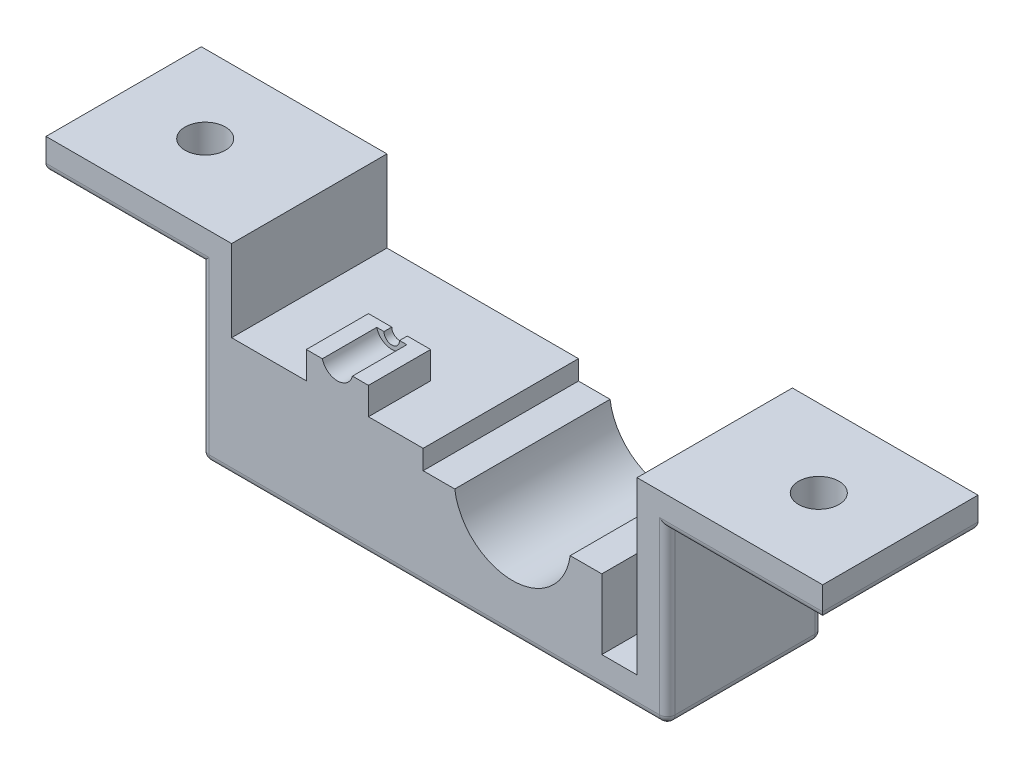
SolidWorks part; units mm, degrees
ref_plane "前视基准面" through (0, 0, 0) normal (0, 0, 1) x (1, 0, 0)
ref_plane "上视基准面" through (0, 0, 0) normal (0, 1, 0) x (1, 0, 0)
ref_plane "右视基准面" through (0, 0, 0) normal (1, 0, 0) x (0, 0, -1)
sketch "草图1" plane through (0, 0, 0) normal (0, 0, 1) x (1, 0, 0)
  line L1 (-24.7617, 11.9489) -> (35.2383, 11.9489)
  line L2 (-24.7617, 11.9489) -> (-24.7617, -14.0511)
  line L3 (-24.7617, -14.0511) -> (35.2383, -14.0511)
  line L4 (35.2383, 11.9489) -> (35.2383, -14.0511)
  dimension "D1" = 60
  dimension "D2" = 26
extrude "凸台-拉伸1" add sketch "草图1" against normal blind 24
sketch "草图2" plane through (0, 0, 0) normal (0, 0, 1) x (1, 0, 0)
  line L0 (-20.7617, -10.0511) -> (31.2383, -10.0511)
  line L1 (-24.7617, 11.9489) -> (-24.7617, -14.0511) construction
  line L2 (35.2383, -14.0511) -> (35.2383, 11.9489) construction
  line L3 (31.2383, 11.9489) -> (31.2383, -10.0511)
  line L4 (35.2383, 11.9489) -> (-24.7617, 11.9489) construction
  line L5 (-20.7617, 11.9489) -> (-20.7617, -10.0511)
  line L6 (-24.7617, -14.0511) -> (35.2383, -14.0511) construction
  dimension "D1" = 4
  dimension "D2" = 4
  dimension "D3" = 4
extrude "切除-拉伸1" cut sketch "草图2" against normal blind 24 and the other way through all
sketch "草图3" plane through (0, -10.0511, 0) normal (0, 1, 0) x (1, 0, 0)
  line L0 (26.7983, 0) -> (26.7983, 24)
  line L1 (-20.7617, 0) -> (31.2383, 0) construction
  line L2 (-20.7617, 24) -> (31.2383, 24) construction
  line L3 (31.2383, 0) -> (31.2383, 24) construction
  line L4 (3.7983, 0) -> (3.7983, 24)
  line L5 (3.7983, 0) -> (26.7983, 0)
  line L6 (26.7983, 24) -> (3.7983, 24)
  dimension "D1" = 4.44
  dimension "D2" = 23
extrude "凸台-拉伸2" add sketch "草图3" along normal blind 10
sketch "草图4" plane through (0, 0, 0) normal (0, 0, 1) x (1, 0, 0)
  line L0 (3.7983, -0.0511) -> (26.7983, -0.0511) construction
  line L1 (7.7983, -0.0511) -> (22.7983, -0.0511)
  arc A0 (7.7983, -0.0511) -> (22.7983, -0.0511) centre (15.2983, -0.0511) ccw
  dimension "D1" = 15
extrude "切除-拉伸2" cut sketch "草图4" against normal through all
sketch "草图5" plane through (0, 0, 0) normal (0, 0, 1) x (1, 0, 0)
  line L0 (3.7983, -1.0511) -> (26.7983, -1.0511)
  line L1 (3.7983, -0.0511) -> (3.7983, -10.0511) construction
  line L2 (26.7983, -0.0511) -> (26.7983, -10.0511) construction
  line L3 (3.7983, -0.0511) -> (7.7983, -0.0511) construction
  line L4 (3.7983, -1.0511) -> (3.7983, -0.0511)
  line L5 (3.7983, -0.0511) -> (26.7983, -0.0511)
  line L6 (26.7983, -0.0511) -> (26.7983, -1.0511)
  dimension "D1" = 1
extrude "切除-拉伸3" cut sketch "草图5" against normal through all
sketch "草图6" plane through (0, -10.0511, 0) normal (0, 1, 0) x (1, 0, 0)
  line L4 (-20.7617, 0) -> (3.7983, 0)
  line L5 (3.7983, 0) -> (3.7983, 24)
  line L6 (3.7983, 24) -> (-20.7617, 24)
  line L7 (-20.7617, 24) -> (-20.7617, 0)
  line L8 (-20.7617, 0) -> (3.7983, 0)
  line L9 (3.7983, 0) -> (3.7983, 24)
  line L10 (3.7983, 24) -> (-20.7617, 24)
  line L11 (-20.7617, 24) -> (-20.7617, 0)
  dimension "D1" = 0
extrude "凸台-拉伸4" add sketch "草图6" along normal blind 15.5
sketch "草图7" plane through (0, 5.4489, 0) normal (0, 1, 0) x (1, 0, 0)
  line L0 (-11.2417, 0) -> (-11.2417, 12)
  line L1 (-20.7617, 0) -> (3.7983, 0) construction
  line L3 (-3.2417, 0) -> (-3.2417, 12)
  line L4 (-20.7617, 24) -> (-20.7617, 0) construction
  line L5 (-11.2417, 12) -> (-3.2417, 12)
  line L6 (-11.2417, 0) -> (-3.2417, 0)
  line L11 (-20.7617, 24) -> (-20.7617, 0)
  line L12 (-20.7617, 0) -> (3.7983, 0)
  line L13 (3.7983, 0) -> (3.7983, 24)
  line L14 (3.7983, 24) -> (-20.7617, 24)
  line L15 (-20.7617, 24) -> (-20.7617, 0)
  line L16 (-20.7617, 0) -> (3.7983, 0)
  line L17 (3.7983, 0) -> (3.7983, 24)
  line L18 (3.7983, 24) -> (-20.7617, 24)
  line M5 (-20.7617, 24) -> (-20.7617, 0)
  line M6 (-20.7617, 0) -> (3.7983, 0)
  line M7 (3.7983, 0) -> (3.7983, 24)
  line M8 (3.7983, 24) -> (-20.7617, 24)
  dimension "D1" = 9.52
  dimension "D2" = 8
  dimension "D3" = 12
  dimension "D4" = 0
extrude "切除-拉伸5" cut sketch "草图7" against normal blind 4 contours L0 L5 L3 M6 M7 M8 M5
sketch "草图8" plane through (0, 0, 0) normal (0, 0, 1) x (1, 0, 0)
  line L0 (-11.2417, 5.4489) -> (-3.2417, 5.4489) construction
  line L1 (-9.2417, 5.4489) -> (-5.2417, 5.4489)
  arc A0 (-9.2417, 5.4489) -> (-5.2417, 5.4489) centre (-7.2417, 5.4489) ccw
  dimension "D1" = 4
extrude "切除-拉伸6" cut sketch "草图8" against normal blind 11
sketch "草图10" plane through (0, 0, 0) normal (0, 0, 1) x (1, 0, 0)
  line L0 (-11.2417, 4.9489) -> (-3.2417, 4.9489)
  line L1 (-11.2417, 1.4489) -> (-11.2417, 5.4489) construction
  line L2 (-3.2417, 1.4489) -> (-3.2417, 5.4489) construction
  line L3 (-11.2417, 5.4489) -> (-9.2417, 5.4489) construction
  line L4 (-3.2417, 4.9489) -> (-3.2417, 5.4489)
  line L5 (-3.2417, 5.4489) -> (-11.2417, 5.4489)
  line L6 (-11.2417, 5.4489) -> (-11.2417, 4.9489)
  dimension "D1" = 0.5
extrude "切除-拉伸8" cut sketch "草图10" against normal through all
sketch "草图11" plane through (0, 0, -12) normal (0, 0, -1) x (-1, 0, 0)
  line L0 (11.2417, 4.9489) -> (3.2417, 4.9489) construction
  circle A0 centre (7.2417, 4.9489) radius 1
  dimension "D1" = 2
extrude "切除-拉伸9" cut sketch "草图11" against normal blind 11
sketch "草图12" plane through (35.2383, 0, 0) normal (1, 0, 0) x (0, 0, -1)
  line L0 (0, 7.9489) -> (24, 7.9489)
  line L1 (0, -14.0511) -> (0, 11.9489) construction
  line L2 (24, -14.0511) -> (24, 11.9489) construction
  line L3 (24, 11.9489) -> (0, 11.9489) construction
  line L4 (0, 7.9489) -> (0, 11.9489)
  line L5 (0, 11.9489) -> (24, 11.9489)
  line L6 (24, 11.9489) -> (24, 7.9489)
  dimension "D1" = 4
extrude "凸台-拉伸5" add sketch "草图12" along normal blind 20
sketch "草图13" plane through (-24.7617, 0, 0) normal (-1, 0, 0) x (0, 0, 1)
  line L0 (-24, 7.9489) -> (0, 7.9489)
  line L1 (-24, 11.9489) -> (-24, -14.0511) construction
  line L2 (0, 11.9489) -> (0, -14.0511) construction
  line L3 (-24, 11.9489) -> (0, 11.9489) construction
  line L4 (-24, 7.9489) -> (-24, 11.9489)
  line L5 (-24, 11.9489) -> (0, 11.9489)
  line L6 (0, 11.9489) -> (0, 7.9489)
  dimension "D1" = 4
extrude "凸台-拉伸6" add sketch "草图13" along normal blind 20
sketch "草图14" plane through (0, 0, 0) normal (0, 0, 1) x (1, 0, 0)
  line L22 (-9.1782, 4.9489) -> (-11.2417, 4.9489)
  line L23 (-11.2417, 4.9489) -> (-11.2417, 1.4489)
  line L24 (-11.2417, 1.4489) -> (-20.7617, 1.4489)
  line L25 (-20.7617, 1.4489) -> (-20.7617, 11.9489)
  line L26 (-20.7617, 11.9489) -> (-44.7617, 11.9489)
  line L27 (-44.7617, 11.9489) -> (-44.7617, 7.9489)
  line L28 (-44.7617, 7.9489) -> (-24.7617, 7.9489)
  line L29 (-24.7617, 7.9489) -> (-24.7617, -14.0511)
  line L30 (-24.7617, -14.0511) -> (35.2383, -14.0511)
  line L31 (35.2383, -14.0511) -> (35.2383, 7.9489)
  line L32 (35.2383, 7.9489) -> (55.2383, 7.9489)
  line L33 (55.2383, 7.9489) -> (55.2383, 11.9489)
  line L34 (55.2383, 11.9489) -> (31.2383, 11.9489)
  line L35 (31.2383, 11.9489) -> (31.2383, -10.0511)
  line L36 (31.2383, -10.0511) -> (26.7983, -10.0511)
  line L37 (26.7983, -10.0511) -> (26.7983, -1.0511)
  line L38 (26.7983, -1.0511) -> (22.7313, -1.0511)
  line L39 (7.8653, -1.0511) -> (3.7983, -1.0511)
  line L40 (3.7983, -1.0511) -> (3.7983, 1.4489)
  line L41 (3.7983, 1.4489) -> (-3.2417, 1.4489)
  line L42 (-3.2417, 1.4489) -> (-3.2417, 4.9489)
  line L43 (-3.2417, 4.9489) -> (-5.3052, 4.9489)
  line L44 (-9.1782, 4.9489) -> (-11.2417, 4.9489)
  line L45 (-11.2417, 4.9489) -> (-11.2417, 1.4489)
  line L46 (-11.2417, 1.4489) -> (-20.7617, 1.4489)
  line L47 (-20.7617, 1.4489) -> (-20.7617, 11.9489)
  line L48 (-20.7617, 11.9489) -> (-44.7617, 11.9489)
  line L49 (-44.7617, 11.9489) -> (-44.7617, 7.9489)
  line L50 (-44.7617, 7.9489) -> (-24.7617, 7.9489)
  line L51 (-24.7617, 7.9489) -> (-24.7617, -14.0511)
  line L52 (-24.7617, -14.0511) -> (35.2383, -14.0511)
  line L53 (35.2383, -14.0511) -> (35.2383, 7.9489)
  line L54 (35.2383, 7.9489) -> (55.2383, 7.9489)
  line L55 (55.2383, 7.9489) -> (55.2383, 11.9489)
  line L56 (55.2383, 11.9489) -> (31.2383, 11.9489)
  line L57 (31.2383, 11.9489) -> (31.2383, -10.0511)
  line L58 (31.2383, -10.0511) -> (26.7983, -10.0511)
  line L59 (26.7983, -10.0511) -> (26.7983, -1.0511)
  line L60 (26.7983, -1.0511) -> (22.7313, -1.0511)
  line L61 (7.8653, -1.0511) -> (3.7983, -1.0511)
  line L62 (3.7983, -1.0511) -> (3.7983, 1.4489)
  line L63 (3.7983, 1.4489) -> (-3.2417, 1.4489)
  line L64 (-3.2417, 1.4489) -> (-3.2417, 4.9489)
  line L65 (-3.2417, 4.9489) -> (-5.3052, 4.9489)
  arc A2 (7.8653, -1.0511) -> (22.7313, -1.0511) centre (15.2983, -0.0511) ccw
  arc A3 (-9.1782, 4.9489) -> (-5.3052, 4.9489) centre (-7.2417, 5.4489) ccw
  arc A4 (7.8653, -1.0511) -> (22.7313, -1.0511) centre (15.2983, -0.0511) ccw
  arc A5 (-9.1782, 4.9489) -> (-5.3052, 4.9489) centre (-7.2417, 5.4489) ccw
  dimension "D1" = 0
extrude "切除-拉伸10" cut sketch "草图14" against normal blind 4
fillet "圆角1" radius 1 14 edges at (-24.7617, -3.0511, -24) (-34.7617, 7.9489, -24) (45.2383, 7.9489, -24) (5.2383, -14.0511, -24) (35.2383, -3.0511, -24) (35.2383, -14.0511, -14) (-24.7617, -14.0511, -14) (-34.7617, 7.9489, -4) (-44.7617, 7.9489, -14) (55.2383, 7.9489, -14) (45.2383, 7.9489, -4) (35.2383, -3.0511, -4) (5.2383, -14.0511, -4) (-24.7617, -3.0511, -4)
sketch "草图15" plane through (0, 7.9489, 0) normal (0, -1, 0) x (-1, 0, 0)
  circle A0 centre (34.2617, 14) radius 2.6
  dimension "D1" = 5.2
extrude "切除-拉伸11" cut sketch "草图15" against normal blind 4
sketch "草图16" plane through (0, 7.9489, 0) normal (0, -1, 0) x (-1, 0, 0)
  circle A0 centre (-44.7383, 14) radius 2.6
  dimension "D1" = 5.2
extrude "切除-拉伸12" cut sketch "草图16" against normal blind 4
sketch "草图17" plane through (31.2383, 0, 0) normal (-1, 0, 0) x (0, 0, 1)
  line L4 (-24, -10.0511) -> (-4, -10.0511)
  line L5 (-4, -10.0511) -> (-4, 11.9489)
  line L6 (-4, 11.9489) -> (-24, 11.9489)
  line L7 (-24, 11.9489) -> (-24, -10.0511)
  line L8 (-24, -10.0511) -> (-4, -10.0511)
  line L9 (-4, -10.0511) -> (-4, 11.9489)
  line L10 (-4, 11.9489) -> (-24, 11.9489)
  line L11 (-24, 11.9489) -> (-24, -10.0511)
  dimension "D1" = 0
extrude "切除-拉伸13" cut sketch "草图17" against normal blind 0.1
sketch "草图18" plane through (-20.7617, 0, 0) normal (1, 0, 0) x (0, 0, -1)
  line L4 (24, 11.9489) -> (4, 11.9489)
  line L5 (4, 11.9489) -> (4, 1.4489)
  line L6 (4, 1.4489) -> (24, 1.4489)
  line L7 (24, 1.4489) -> (24, 11.9489)
  line L8 (24, 11.9489) -> (4, 11.9489)
  line L9 (4, 11.9489) -> (4, 1.4489)
  line L10 (4, 1.4489) -> (24, 1.4489)
  line L11 (24, 1.4489) -> (24, 11.9489)
  dimension "D1" = 0
extrude "切除-拉伸14" cut sketch "草图18" against normal blind 0.1
